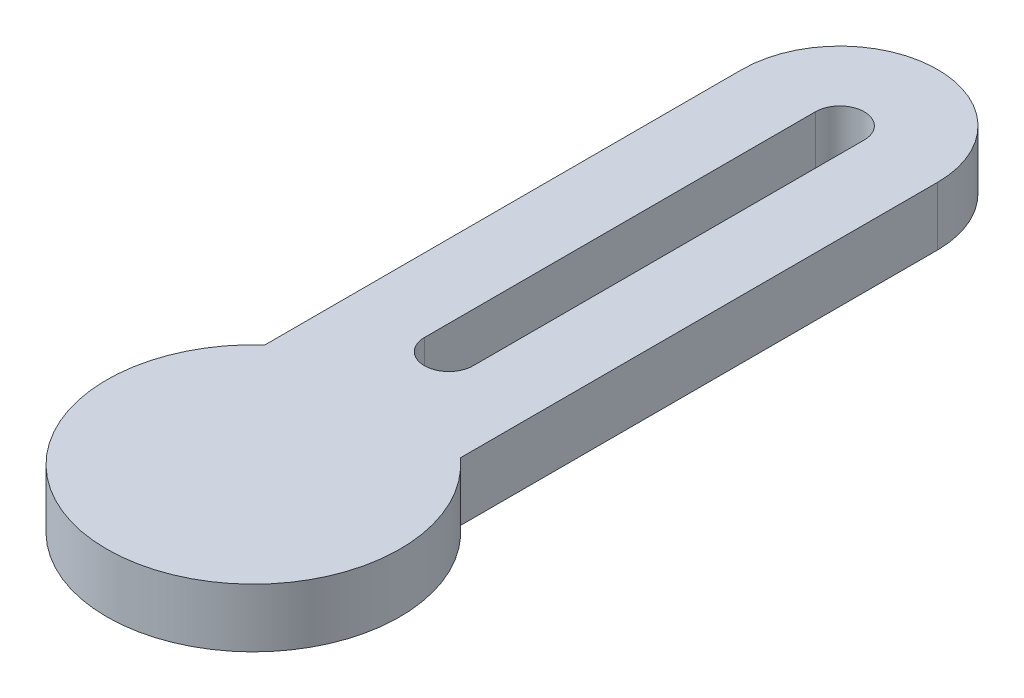
SolidWorks part; units mm, degrees
ref_plane "Front Plane" through (0, 0, 0) normal (0, 0, 1) x (1, 0, 0)
ref_plane "Top Plane" through (0, 0, 0) normal (0, 1, 0) x (1, 0, 0)
ref_plane "Right Plane" through (0, 0, 0) normal (1, 0, 0) x (0, 0, -1)
sketch "Sketch1" plane through (0, 0, 0) normal (0, 1, 0) x (1, 0, 0)
  line L0 (0, 0) -> (0, 30) construction
  line L1 (-5, 0) -> (-5, 30)
  line L2 (5, 0) -> (5, 30)
  line L3 (0, 30) -> (0, 10) construction
  line L4 (1.25, 30) -> (1.25, 10)
  line L5 (-1.25, 30) -> (-1.25, 10)
  arc A0 (-5, 0) -> (5, 0) centre (0, 0) ccw
  arc A1 (5, 30) -> (-5, 30) centre (0, 30) ccw
  arc A2 (1.25, 30) -> (-1.25, 30) centre (0, 30) ccw
  arc A3 (-1.25, 10) -> (1.25, 10) centre (0, 10) ccw
  circle A4 centre (0, 0) radius 7.5
  point P2 (0, 15)
  point P11 (0, 20)
extrude "Boss-Extrude1" add sketch "Sketch1" along normal blind 3 contours A4 L2 A1 L1 A3 L5 A2 L4 | L2 A4 L1 A0 | L1 A4 L2 A0
